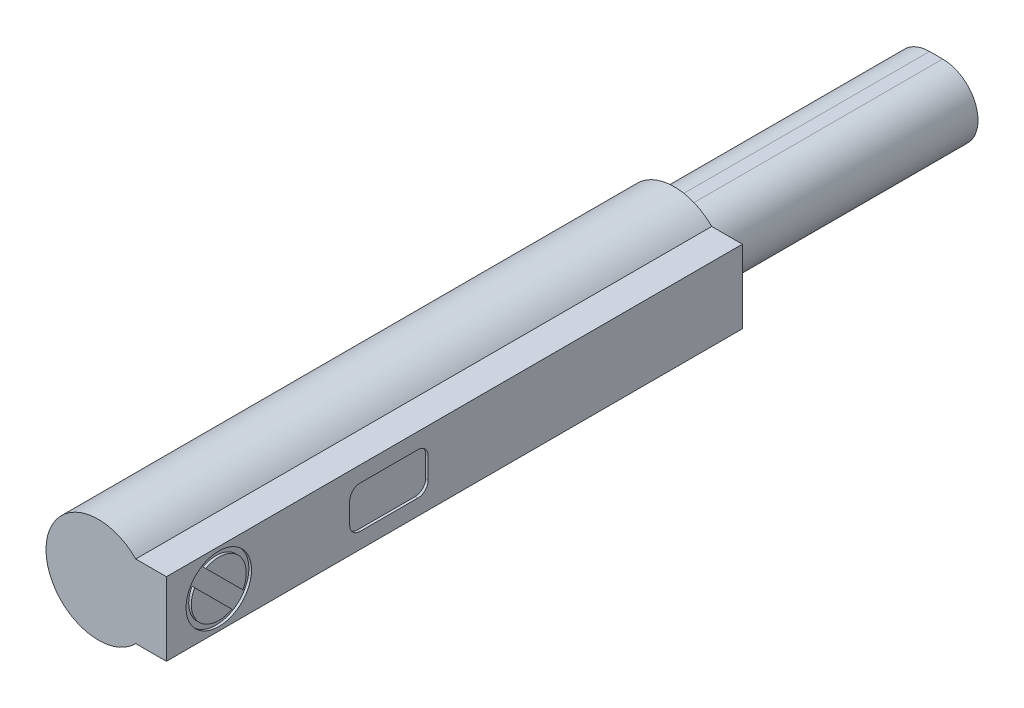
SolidWorks part; units mm, degrees
ref_plane "前视基准面" through (0, 0, 0) normal (0, 0, 1) x (1, 0, 0)
ref_plane "上视基准面" through (0, 0, 0) normal (0, 1, 0) x (1, 0, 0)
ref_plane "右视基准面" through (0, 0, 0) normal (1, 0, 0) x (0, 0, -1)
ref_plane "基准面4" through (0, 0, 0) normal (0, 0, 1) x (1, 0, 0)
sketch "草图1" plane through (0, 0, 0) normal (0, 0, 1) x (1, 0, 0)
  line L0 (1.4283, -1.4) -> (2.6, -1.4)
  line L1 (2.6, -1.4) -> (2.6, 1.4)
  line L2 (2.6, 1.4) -> (1.4283, 1.4)
  arc A0 (1.4283, 1.4) -> (1.4283, -1.4) centre (0, 0) ccw
extrude "凸台-拉伸1" add sketch "草图1" against normal blind 22
ref_plane "基准面5" through (0, 0, -22) normal (0, 0, 1) x (1, 0, 0)
sketch "草图2" plane through (0, 0, -22) normal (0, 0, 1) x (1, 0, 0)
  line L0 (-0.25, -1.35) -> (0.25, -1.35)
  line L1 (0.25, 1.35) -> (-0.25, 1.35)
  arc A0 (-0.25, 1.35) -> (-0.25, -1.35) centre (-0.25, 0) ccw
  arc A1 (0.25, -1.35) -> (0.25, 1.35) centre (0.25, 0) ccw
extrude "凸台-拉伸2" add sketch "草图2" against normal blind 10
ref_plane "基准面6" through (2.6, 0, 0) normal (1, 0, 0) x (0, 0, -1)
sketch "草图3" plane through (2.6, 0, 0) normal (1, 0, 0) x (0, 0, -1)
  circle A0 centre (2, 0) radius 1.25
  circle A1 centre (2, 0) radius 1.05
extrude "切除-拉伸1" cut sketch "草图3" against normal blind 0.1
ref_plane "基准面7" through (2.6, 0, 0) normal (1, 0, 0) x (0, 0, -1)
sketch "草图4" plane through (2.6, 0, 0) normal (1, 0, 0) x (0, 0, -1)
  line L0 (7.4, -0.8) -> (9.6, -0.8)
  line L1 (10, -0.4) -> (10, 0.4)
  line L2 (9.6, 0.8) -> (7.4, 0.8)
  line L3 (7, 0.4) -> (7, -0.4)
  arc A0 (7, -0.4) -> (7.4, -0.8) centre (7.4, -0.4) ccw
  arc A1 (9.6, -0.8) -> (10, -0.4) centre (9.6, -0.4) ccw
  arc A2 (10, 0.4) -> (9.6, 0.8) centre (9.6, 0.4) ccw
  arc A3 (7.4, 0.8) -> (7, 0.4) centre (7.4, 0.4) ccw
extrude "切除-拉伸2" cut sketch "草图4" against normal blind 0.1
ref_plane "基准面8" through (2.6, 0, 0) normal (1, 0, 0) x (0, 0, -1)
sketch "草图5" plane through (2.6, 0, 0) normal (1, 0, 0) x (0, 0, -1)
  line L0 (0.9663, 0.6095) -> (2.6095, -1.0337)
  line L1 (3.0337, -0.6095) -> (1.3905, 1.0337)
  arc A0 (2.6095, -1.0337) -> (3.0337, -0.6095) centre (2, 0) ccw
  arc A1 (1.3905, 1.0337) -> (0.9663, 0.6095) centre (2, 0) ccw
extrude "切除-拉伸3" cut sketch "草图5" against normal blind 0.1
